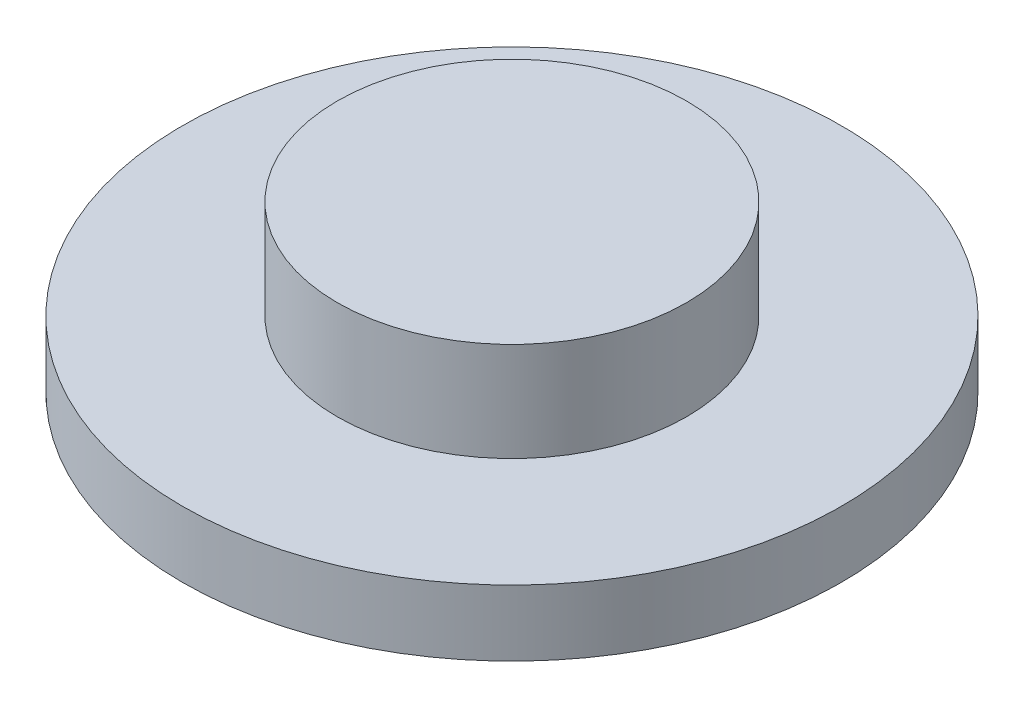
SolidWorks part; units mm, degrees
ref_plane "前视基准面" through (0, 0, 0) normal (0, 0, 1) x (1, 0, 0)
ref_plane "上视基准面" through (0, 0, 0) normal (0, 1, 0) x (1, 0, 0)
ref_plane "右视基准面" through (0, 0, 0) normal (1, 0, 0) x (0, 0, -1)
other "Configuration Table"
sketch "草图1" plane through (0, 0, 0) normal (0, 1, 0) x (1, 0, 0)
  circle A0 centre (0, 0) radius 15
  dimension "D1" = 30
extrude "凸台-拉伸1" add sketch "草图1" along normal blind 3
sketch "草图2" plane through (0, 3, 0) normal (0, 1, 0) x (1, 0, 0)
  circle A0 centre (0, 0) radius 7.95
  dimension "D1" = 15.9
extrude "凸台-拉伸2" add sketch "草图2" along normal blind 4.5
